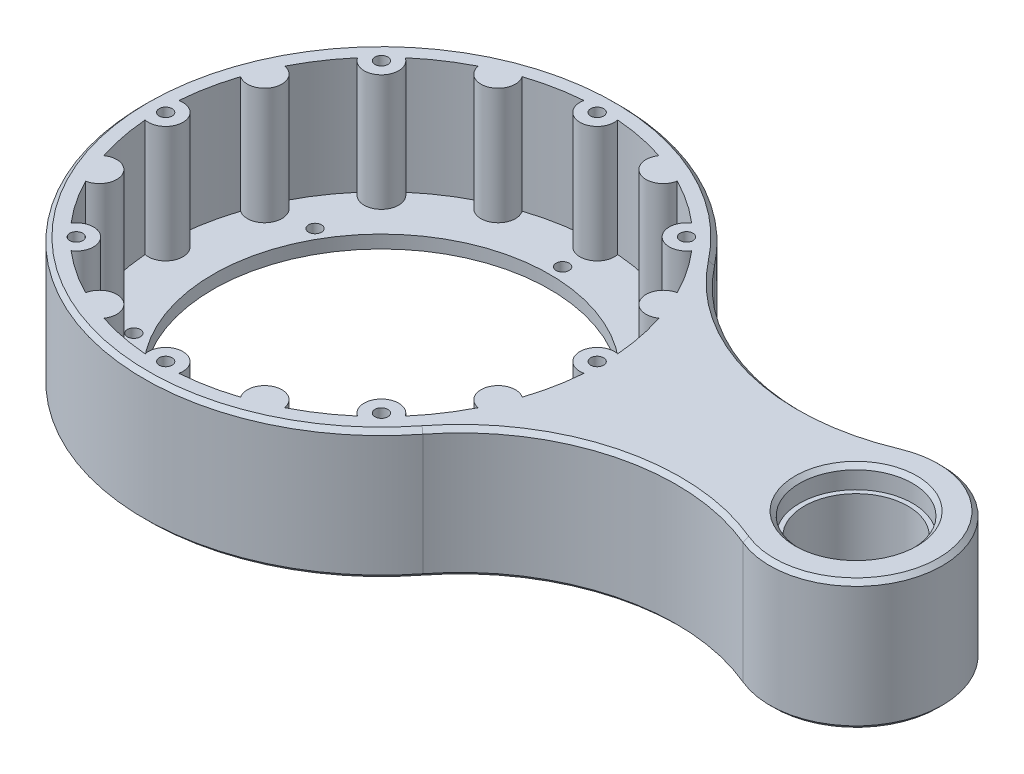
SolidWorks part; units mm, degrees
ref_plane "Front Plane" through (0, 0, 0) normal (0, 0, 1) x (1, 0, 0)
ref_plane "Top Plane" through (0, 0, 0) normal (0, 1, 0) x (1, 0, 0)
ref_plane "Right Plane" through (0, 0, 0) normal (1, 0, 0) x (0, 0, -1)
sketch "Sketch1" plane through (0, 0, 0) normal (0, 1, 0) x (1, 0, 0)
  circle A0 centre (0, 0) radius 39
  circle A1 centre (0, 0) radius 55
  circle A2 centre (0, 50) radius 1.5
  circle A3 centre (35.3553, 35.3553) radius 1.5
  circle A4 centre (50, 0) radius 1.5
  circle A5 centre (35.3553, -35.3553) radius 1.5
  circle A6 centre (0, -50) radius 1.5
  circle A7 centre (-35.3553, -35.3553) radius 1.5
  circle A8 centre (-50, 0) radius 1.5
  circle A9 centre (-35.3553, 35.3553) radius 1.5
  circle A18 centre (0, 42) radius 1.5
  circle A19 centre (36.3731, 21) radius 1.5
  circle A20 centre (36.3731, -21) radius 1.5
  circle A21 centre (0, -42) radius 1.5
  circle A22 centre (-36.3731, -21) radius 1.5
  circle A23 centre (-36.3731, 21) radius 1.5
  point P22 (0, 0)
  point P35 (0, 0)
  point P39 (0, 0)
  dimension "D1" = 110
  dimension "D2" = 78
  dimension "D3" = 3
  dimension "D6" = 42
  dimension "D7" = 3
  dimension "D4" = 50
  dimension "D5" = 8
  dimension "D8" = 6
extrude "Boss-Extrude1" add sketch "Sketch1" along normal blind 3
sketch "Sketch2" plane through (0, 3, 0) normal (0, 1, 0) x (1, 0, 0)
  arc A0 (-3.9086, 50.85) -> (3.9086, 50.85) centre (0, 50) ccw
  arc A1 (15.8483, 48.475) -> (23.0706, 45.4835) centre (19.1342, 46.194) ccw
  arc A2 (33.1926, 38.7202) -> (38.7202, 33.1926) centre (35.3553, 35.3553) ccw
  arc A3 (45.4835, 23.0706) -> (48.475, 15.8483) centre (46.194, 19.1342) ccw
  arc A4 (50.85, 3.9086) -> (50.85, -3.9086) centre (50, 0) ccw
  arc A5 (48.475, -15.8483) -> (45.4835, -23.0706) centre (46.194, -19.1342) ccw
  arc A6 (38.7202, -33.1926) -> (33.1926, -38.7202) centre (35.3553, -35.3553) ccw
  arc A7 (23.0706, -45.4835) -> (15.8483, -48.475) centre (19.1342, -46.194) ccw
  arc A8 (3.9086, -50.85) -> (-3.9086, -50.85) centre (0, -50) ccw
  arc A9 (-15.8483, -48.475) -> (-23.0706, -45.4835) centre (-19.1342, -46.194) ccw
  arc A10 (-33.1926, -38.7202) -> (-38.7202, -33.1926) centre (-35.3553, -35.3553) ccw
  arc A11 (-45.4835, -23.0706) -> (-48.475, -15.8483) centre (-46.194, -19.1342) ccw
  arc A12 (-50.85, -3.9086) -> (-50.85, 3.9086) centre (-50, 0) ccw
  arc A13 (-48.475, 15.8483) -> (-45.4835, 23.0706) centre (-46.194, 19.1342) ccw
  arc A14 (-38.7202, 33.1926) -> (-33.1926, 38.7202) centre (-35.3553, 35.3553) ccw
  arc A15 (-23.0706, 45.4835) -> (-15.8483, 48.475) centre (-19.1342, 46.194) ccw
  arc A16 (-48.475, 15.8483) -> (-50.85, 3.9086) centre (0, 0) ccw
  arc A17 (-50.85, -3.9086) -> (-48.475, -15.8483) centre (0, 0) ccw
  arc A18 (-45.4835, -23.0706) -> (-38.7202, -33.1926) centre (0, 0) ccw
  arc A19 (-33.1926, -38.7202) -> (-23.0706, -45.4835) centre (0, 0) ccw
  arc A20 (-15.8483, -48.475) -> (-3.9086, -50.85) centre (0, 0) ccw
  arc A21 (3.9086, -50.85) -> (15.8483, -48.475) centre (0, 0) ccw
  arc A22 (23.0706, -45.4835) -> (33.1926, -38.7202) centre (0, 0) ccw
  arc A23 (38.7202, -33.1926) -> (45.4835, -23.0706) centre (0, 0) ccw
  arc A24 (48.475, -15.8483) -> (50.85, -3.9086) centre (0, 0) ccw
  arc A25 (50.85, 3.9086) -> (48.475, 15.8483) centre (0, 0) ccw
  arc A26 (45.4835, 23.0706) -> (38.7202, 33.1926) centre (0, 0) ccw
  arc A27 (33.1926, 38.7202) -> (23.0706, 45.4835) centre (0, 0) ccw
  arc A28 (15.8483, 48.475) -> (3.9086, 50.85) centre (0, 0) ccw
  arc A29 (-3.9086, 50.85) -> (-15.8483, 48.475) centre (0, 0) ccw
  arc A30 (-23.0706, 45.4835) -> (-33.1926, 38.7202) centre (0, 0) ccw
  arc A31 (-38.7202, 33.1926) -> (-45.4835, 23.0706) centre (0, 0) ccw
  circle A32 centre (0, 0) radius 55 construction
  circle A33 centre (0, 0) radius 55
  circle A34 centre (-35.3553, 35.3553) radius 1.5 construction
  circle A35 centre (-50, 0) radius 1.5 construction
  circle A36 centre (-35.3553, -35.3553) radius 1.5 construction
  circle A37 centre (0, -50) radius 1.5 construction
  circle A38 centre (35.3553, -35.3553) radius 1.5 construction
  circle A39 centre (50, 0) radius 1.5 construction
  circle A40 centre (35.3553, 35.3553) radius 1.5 construction
  circle A41 centre (0, 50) radius 1.5 construction
  circle A42 centre (-35.3553, 35.3553) radius 1.5
  circle A43 centre (-50, 0) radius 1.5
  circle A44 centre (-35.3553, -35.3553) radius 1.5
  circle A45 centre (0, -50) radius 1.5
  circle A46 centre (35.3553, -35.3553) radius 1.5
  circle A47 centre (50, 0) radius 1.5
  circle A48 centre (35.3553, 35.3553) radius 1.5
  circle A49 centre (0, 50) radius 1.5
  point P35 (0, 0)
  dimension "D1" = 8
  dimension "D4" = 102
  dimension "D2" = 50
  dimension "D3" = 16
extrude "Boss-Extrude3" add sketch "Sketch2" along normal blind 27
sketch "Sketch3" plane through (0, 30, 0) normal (0, 1, 0) x (1, 0, 0)
  circle A0 centre (0, 0) radius 55 construction
  arc A1 (43.3929, -33.7944) -> (43.3929, 33.7944) centre (0, 0) ccw
  arc A5 (102.2403, -18.4333) -> (102.2403, 18.4333) centre (110, 0) ccw
  circle A6 centre (110, 0) radius 13.1
  arc A7 (43.3929, -33.7944) -> (102.2403, -18.4333) centre (82.8409, -64.5165) cw
  arc A8 (43.3929, 33.7944) -> (102.2403, 18.4333) centre (82.8409, 64.5165) ccw
  dimension "D1" = 40
  dimension "D4" = 50
  dimension "D2" = 26.2
  dimension "D5" = 50
  dimension "D3" = 110
extrude "Boss-Extrude4" add sketch "Sketch3" along normal blind 30 from surface at -30 starting at face at (0, 0, 55)
sketch "Sketch6" plane through (0, 30, 0) normal (0, 1, 0) x (1, 0, 0)
  circle A0 centre (110, 0) radius 12
  circle A1 centre (110, 0) radius 13.1 construction
  circle A2 centre (110, 0) radius 13.1
  dimension "D1" = 24
extrude "Boss-Extrude5" add sketch "Sketch6" against normal blind 20 from offset 5 offset against normal yes
chamfer "Chamfer1" distance 1 angle 45 10 edges at (110, 30, 13.1) (110, 0, 13.1) (70.2124, 0, -16.1376) (70.2124, 30, -16.1376) (130, 0, 0) (130, 30, 0) (70.2124, 0, 16.1376) (70.2124, 30, 16.1376) (-55, 0, 0) (-55, 30, 0)
